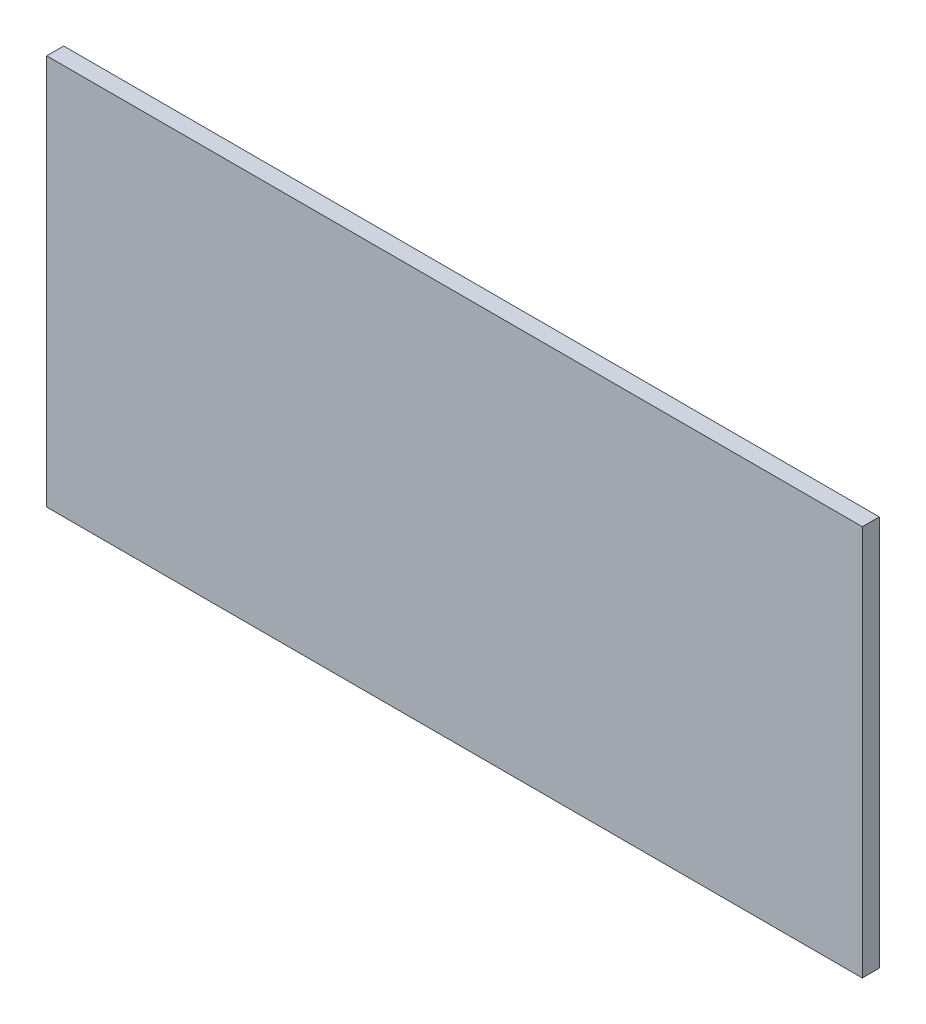
SolidWorks part; units mm, degrees
ref_plane "Front Plane" through (0, 0, 0) normal (0, 0, 1) x (1, 0, 0)
ref_plane "Top Plane" through (0, 0, 0) normal (0, 1, 0) x (1, 0, 0)
ref_plane "Right Plane" through (0, 0, 0) normal (1, 0, 0) x (0, 0, -1)
sketch "Sketch1" plane through (0, 0, 0) normal (0, 0, 1) x (1, 0, 0)
  line L1 (0, 0) -> (609.6, 0)
  line L2 (0, 0) -> (0, 292.1)
  line L3 (0, 292.1) -> (609.6, 292.1)
  line L4 (609.6, 0) -> (609.6, 292.1)
  dimension "D1" = 609.6
  dimension "D2" = 292.1
extrude "Boss-Extrude1" add sketch "Sketch1" along normal blind 12.7
